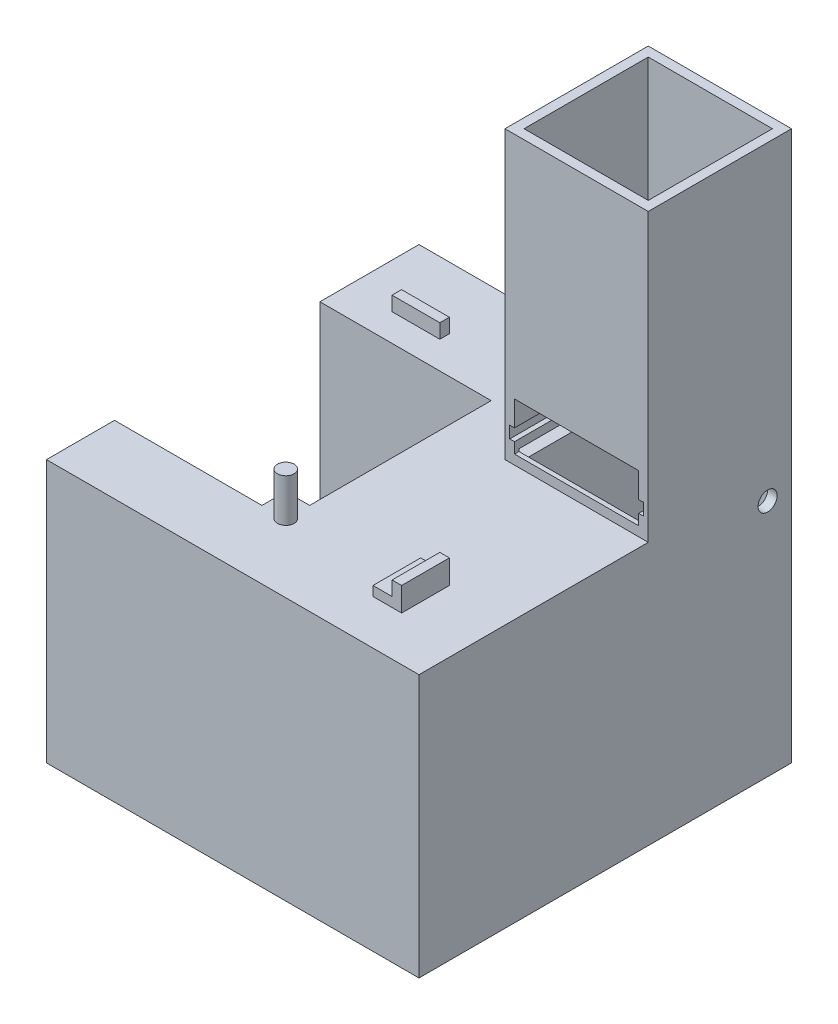
SolidWorks part; units mm, degrees
ref_plane "Front Plane" through (0, 0, 0) normal (0, 0, 1) x (1, 0, 0)
ref_plane "Top Plane" through (0, 0, 0) normal (0, 1, 0) x (1, 0, 0)
ref_plane "Right Plane" through (0, 0, 0) normal (1, 0, 0) x (0, 0, -1)
sketch "Sketch1" plane through (0, 0, 0) normal (0, 1, 0) x (1, 0, 0)
  line L1 (-39, -39) -> (39, -39)
  line L2 (-39, -39) -> (-39, 39)
  line L3 (-39, 39) -> (39, 39)
  line L4 (39, -39) -> (39, 39)
  line L5 (-39, -39) -> (39, 39) construction
  line L6 (-39, 39) -> (39, -39) construction
  point P0 (0, 0)
  dimension "D1" = 78
  dimension "D2" = 78
extrude "Boss-Extrude1" add sketch "Sketch1" along normal blind 2
sketch "Sketch2" plane through (0, 2, 0) normal (0, 1, 0) x (1, 0, 0)
  line L1 (39, 39) -> (9, 39)
  line L2 (39, 39) -> (39, 9)
  line L3 (39, 9) -> (9, 9)
  line L4 (9, 39) -> (9, 9)
  dimension "D1" = 30
  dimension "D2" = 30
extrude "Boss-Extrude2" add sketch "Sketch2" along normal blind 60
sketch "Sketch3" plane through (0, 62, 0) normal (0, 1, 0) x (1, 0, 0)
  line L2 (11, 11) -> (37, 11)
  line L3 (11, 11) -> (11, 37)
  line L4 (11, 37) -> (37, 37)
  line L5 (37, 11) -> (37, 37)
  line L6 (11, 11) -> (37, 37) construction
  line L7 (11, 37) -> (37, 11) construction
  point P4 (24, 24)
  dimension "D1" = 26
extrude "Cut-Extrude1" cut sketch "Sketch3" against normal blind 62
sketch "Sketch4" plane through (9, 0, 0) normal (-1, 0, 0) x (0, 0, 1)
  line L3 (-37.9345, 2) -> (-9.9345, 2)
  line L4 (-37.9345, 2) -> (-37.9345, 4.5)
  line L5 (-37.9345, 4.5) -> (-9.9345, 4.5)
  line L6 (-9.9345, 2) -> (-9.9345, 4.5)
  line L7 (-37.9345, 2) -> (-9.9345, 4.5) construction
  line L8 (-37.9345, 4.5) -> (-9.9345, 2) construction
  point P4 (-23.9345, 3.25)
  dimension "D2" = 28
extrude "Cut-Extrude2" cut sketch "Sketch4" against normal blind 28
sketch "Sketch5" plane through (0, 0, -9) normal (0, 0, 1) x (1, 0, 0)
  line L1 (37, 2) -> (37, 4.5) construction
  line L2 (11, 4.5) -> (11, 62) construction
  line L3 (37, 4) -> (11, 4)
  line L4 (37, 4) -> (37, 14)
  line L5 (37, 14) -> (11, 14)
  line L6 (11, 4) -> (11, 14)
  dimension "D2" = 10
extrude "Cut-Extrude3" cut sketch "Sketch5" against normal blind 2
sketch "Sketch6" plane through (37, 0, 0) normal (-1, 0, 0) x (0, 0, 1)
  line L1 (-9, 4) -> (-9, 14) construction
  line L3 (-37, 4.5) -> (-37, 62) construction
  line L4 (-9, 6.25) -> (-37, 6.25)
  line L5 (-9, 6.25) -> (-9, 8.75)
  line L6 (-9, 8.75) -> (-37, 8.75)
  line L7 (-37, 6.25) -> (-37, 8.75)
  dimension "D2" = 2.5
extrude "Cut-Extrude4" cut sketch "Sketch6" against normal blind 1
sketch "Sketch7" plane through (11, 0, 0) normal (1, 0, 0) x (0, 0, -1)
  line L1 (37, 8.75) -> (9, 8.75)
  line L2 (37, 8.75) -> (37, 6.25)
  line L3 (37, 6.25) -> (9, 6.25)
  line L4 (9, 8.75) -> (9, 6.25)
extrude "Cut-Extrude5" cut sketch "Sketch7" against normal blind 1
sketch "Sketch14" plane through (0, 2, 0) normal (0, 1, 0) x (1, 0, 0)
  line L0 (9, 9) -> (39, 9)
  line L1 (24, 9) -> (24, -24.64)
  line L2 (24, -24.64) -> (-3.25, -24.64)
  circle A0 centre (-3.25, -24.64) radius 1.75
  dimension "D3" = 3.5
  dimension "D1" = 33.64
  dimension "D2" = 27.25
extrude "Boss-Extrude8" add sketch "Sketch14" along normal blind 5 contours A0
sketch "Sketch15" plane through (0, 2, 0) normal (0, 1, 0) x (1, 0, 0)
  line L0 (9, 39) -> (9, 9)
  line L1 (9, 24) -> (-24.64, 24)
  line L2 (-24.64, 24) -> (-24.64, -3.25)
  line L3 (-24.64, 24) -> (-24.64, -3.25)
  line L9 (-46.14, -24.75) -> (-3.14, -24.75)
  line L10 (-46.14, -24.75) -> (-46.14, 18.25)
  line L11 (-46.14, 18.25) -> (-3.14, 18.25)
  line L12 (-3.14, -24.75) -> (-3.14, 18.25)
  line L13 (-46.14, -24.75) -> (-3.14, 18.25) construction
  line L14 (-46.14, 18.25) -> (-3.14, -24.75) construction
  circle A0 centre (-24.64, -3.25) radius 1.75
  dimension "D3" = 3.5
  dimension "D1" = 33.64
  dimension "D2" = 27.25
  dimension "D4" = 43
  dimension "D5" = 43
sketch "Sketch16" plane through (0, 2, 0) normal (0, 1, 0) x (1, 0, 0)
  line L0 (24, 9) -> (24, -24.64)
  line L1 (9, 9) -> (39, 9) construction
  line L3 (24, -24.64) -> (20, -24.64)
  line L4 (24, -24.64) -> (24, -19.64)
  line L5 (24, -19.64) -> (20, -19.64)
  line L6 (20, -24.64) -> (20, -19.64)
  line L7 (24, -24.64) -> (20, -24.64)
  line L8 (24, -24.64) -> (24, -29.64)
  line L9 (24, -29.64) -> (20, -29.64)
  line L10 (20, -24.64) -> (20, -29.64)
  dimension "D1" = 33.64
  dimension "D2" = 5
  dimension "D3" = 4
  dimension "D4" = 5
extrude "Boss-Extrude10" add sketch "Sketch16" along normal blind 2 contours L6 L3 L0 L5 | L3 L10 L9 L8
sketch "Sketch17" plane through (0, 2, 0) normal (0, 1, 0) x (1, 0, 0)
  line L1 (24, -19.64) -> (26, -19.64)
  line L2 (24, -19.64) -> (24, -29.64)
  line L3 (24, -29.64) -> (26, -29.64)
  line L4 (26, -19.64) -> (26, -29.64)
  dimension "D1" = 10
  dimension "D2" = 2
extrude "Boss-Extrude11" add sketch "Sketch17" along normal blind 5
sketch "Sketch18" plane through (0, 2, 0) normal (0, 1, 0) x (1, 0, 0)
  line L0 (9, 24) -> (-19.64, 24)
  line L1 (9, 39) -> (9, 9) construction
  line L3 (-19.64, 24) -> (-29.64, 24)
  line L4 (-19.64, 24) -> (-19.64, 26)
  line L5 (-19.64, 26) -> (-29.64, 26)
  line L6 (-29.64, 24) -> (-29.64, 26)
  dimension "D1" = 28.64
  dimension "D2" = 2
  dimension "D3" = 10
extrude "Boss-Extrude12" add sketch "Sketch18" along normal blind 3 contours L6 L3 L4 L5
sketch "Sketch21" plane through (0, 0, 0) normal (0, -1, 0) x (1, 0, 0)
  line L1 (-39, 39) -> (39, 39)
  line L2 (-39, 39) -> (-39, -39)
  line L3 (-39, -39) -> (39, -39)
  line L4 (39, 39) -> (39, -39)
extrude "Boss-Extrude13" add sketch "Sketch21" along normal blind 53
extrude "Cut-Extrude6" cut sketch "Sketch15" against normal blind 53 contours L11 L12 L9 L10
sketch "Sketch23" plane through (-3.14, 0, 0) normal (-1, 0, 0) x (0, 0, 1)
  line L1 (24.75, 2) -> (19.75, 2)
  line L2 (24.75, 2) -> (24.75, 0)
  line L3 (24.75, 0) -> (19.75, 0)
  line L4 (19.75, 2) -> (19.75, 0)
  dimension "D1" = 5
extrude "Boss-Extrude15" add sketch "Sketch23" along normal blind 5
sketch "Sketch24" plane through (0, 0, 0) normal (0, 1, 0) x (1, 0, 0)
  line L1 (11, 37) -> (37, 37)
  line L2 (11, 37) -> (11, 11)
  line L3 (11, 11) -> (37, 11)
  line L4 (37, 37) -> (37, 11)
extrude "Cut-Extrude9" cut sketch "Sketch24" against normal blind 51
sketch "Sketch27" plane through (0, 0, -39) normal (0, 0, -1) x (-1, 0, 0)
  line L0 (-11, -51) -> (-11, 2) construction
  line L1 (-37, -51) -> (-11, -51)
  line L2 (-37, -51) -> (-37, -25)
  line L3 (-37, -25) -> (-11, -25)
  line L4 (-11, -51) -> (-11, -25)
  dimension "D1" = 26
extrude "Cut-Extrude10" cut sketch "Sketch27" against normal blind 2
sketch "Sketch28" plane through (11, 0, 0) normal (1, 0, 0) x (0, 0, -1)
  line L0 (39, -51) -> (11, -51)
  line L1 (11, -51) -> (11, -24.5)
  line L2 (11, -51) -> (11, 2) construction
  line L3 (11, -24.5) -> (39, -51)
extrude "Boss-Extrude16" add sketch "Sketch28" along normal blind 26
sketch "Sketch31" plane through (0, 2, 0) normal (0, 1, 0) x (1, 0, 0)
  line L1 (9, 39) -> (-4, 39)
  line L2 (9, 39) -> (9, 26)
  line L3 (9, 26) -> (-4, 26)
  line L4 (-4, 39) -> (-4, 26)
  dimension "D1" = 13
  dimension "D2" = 13
extrude "Cut-Extrude12" cut sketch "Sketch31" against normal blind 10
sketch "Sketch32" plane through (39, 0, 0) normal (1, 0, 0) x (0, 0, -1)
  line L0 (37, 2) -> (34, 2)
  line L1 (37, 2) -> (11, 2) construction
  line L2 (34, 2) -> (34, -3)
  circle A0 centre (34, -3) radius 2
  dimension "D3" = 4
  dimension "D1" = 3
  dimension "D2" = 5
extrude "Cut-Extrude13" cut sketch "Sketch32" against normal blind 2
sketch "Sketch33" plane through (11, 0, 0) normal (1, 0, 0) x (0, 0, -1)
  circle A0 centre (34, -3) radius 2
extrude "Cut-Extrude14" cut sketch "Sketch33" against normal blind 2
sketch "Sketch36" plane through (0, 7, 0) normal (0, 1, 0) x (1, 0, 0)
  circle A0 centre (-3.25, -24.64) radius 1.75
extrude "Boss-Extrude17" add sketch "Sketch36" along normal blind 4
